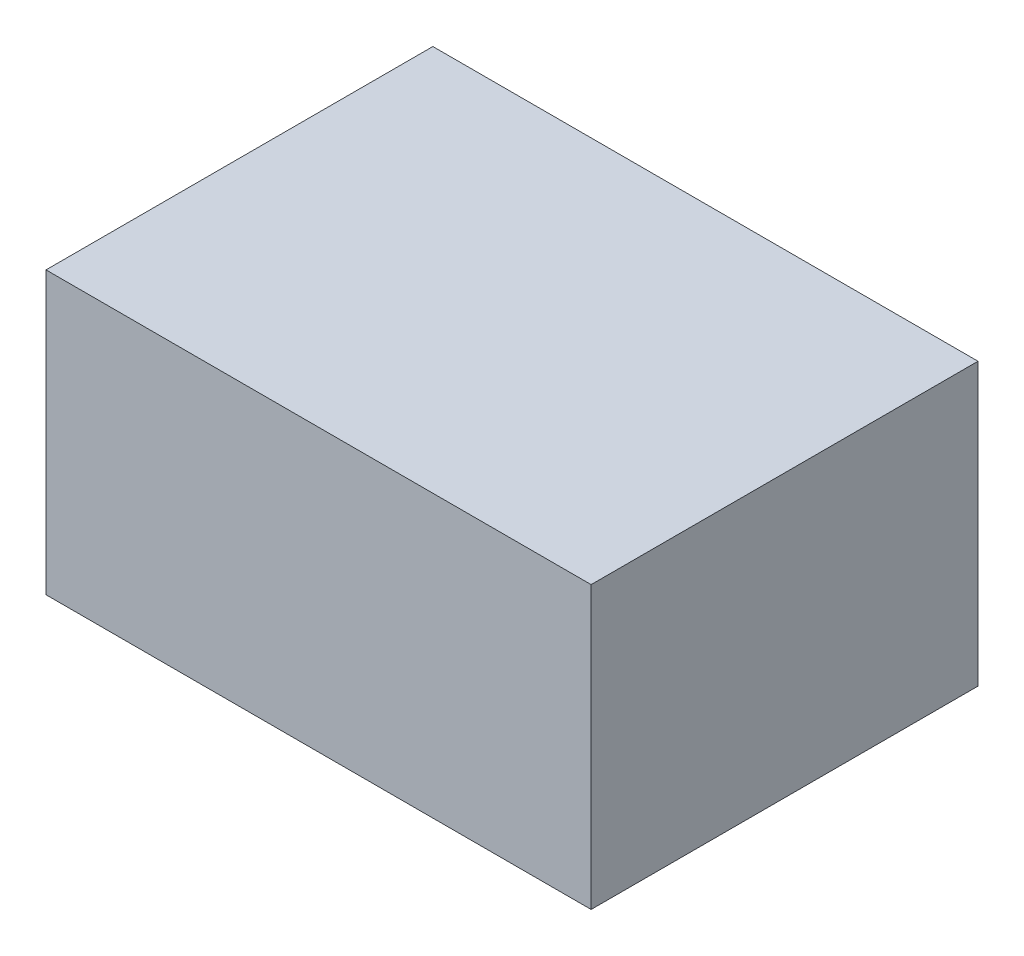
SolidWorks part; units mm, degrees
ref_plane "Front Plane" through (0, 0, 0) normal (0, 0, 1) x (1, 0, 0)
ref_plane "Top Plane" through (0, 0, 0) normal (0, 1, 0) x (1, 0, 0)
ref_plane "Right Plane" through (0, 0, 0) normal (1, 0, 0) x (0, 0, -1)
sketch "Sketch1" plane through (0, 0, 0) normal (0, 1, 0) x (1, 0, 0)
  line L1 (0, 0) -> (62, 0)
  line L2 (0, 0) -> (0, 44)
  line L3 (0, 44) -> (62, 44)
  line L4 (62, 0) -> (62, 44)
extrude "Boss-Extrude1" add sketch "Sketch1" along normal blind 32
